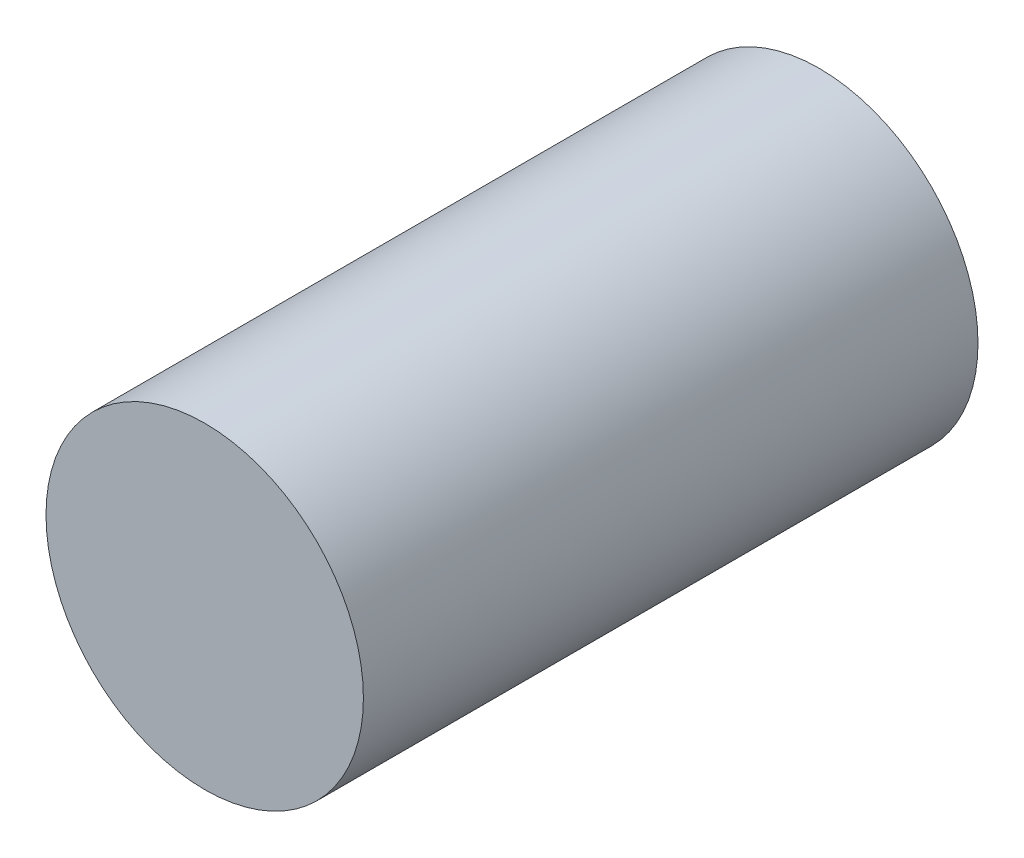
SolidWorks part; units mm, degrees
ref_plane "Front Plane" through (0, 0, 0) normal (0, 0, 1) x (1, 0, 0)
ref_plane "Top Plane" through (0, 0, 0) normal (0, 1, 0) x (1, 0, 0)
ref_plane "Right Plane" through (0, 0, 0) normal (1, 0, 0) x (0, 0, -1)
sketch "Sketch1" plane through (0, 0, 0) normal (0, 0, 1) x (1, 0, 0)
  circle A0 centre (0, 0) radius 3.925
  dimension "D1" = 7.85
extrude "Boss-Extrude1" add sketch "Sketch1" along normal blind 15.2
